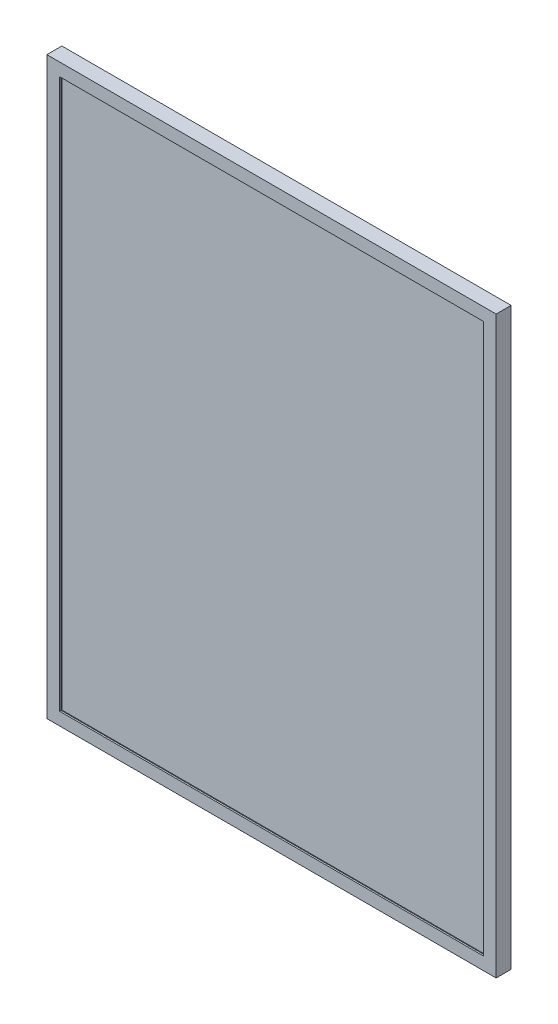
SolidWorks part; units mm, degrees
ref_plane "Front Plane" through (0, 0, 0) normal (0, 0, 1) x (1, 0, 0)
ref_plane "Top Plane" through (0, 0, 0) normal (0, 1, 0) x (1, 0, 0)
ref_plane "Right Plane" through (0, 0, 0) normal (1, 0, 0) x (0, 0, -1)
sketch "Sketch1" plane through (0, 0, 0) normal (0, 0, 1) x (1, 0, 0)
  line L1 (300, -384) -> (-300, -384)
  line L2 (300, -384) -> (300, 384)
  line L3 (300, 384) -> (-300, 384)
  line L4 (-300, -384) -> (-300, 384)
  line L5 (300, -384) -> (-300, 384) construction
  line L6 (300, 384) -> (-300, -384) construction
  point P0 (0, 0)
  dimension "D1" = 600
  dimension "D2" = 768
extrude "Boss-Extrude1" add sketch "Sketch1" along normal blind 20
shell "Shell1" thickness 2
sketch "Sketch2" plane through (0, 0, 20) normal (0, 0, 1) x (1, 0, 0)
  line L1 (-298, 382) -> (298, 382)
  line L2 (-298, 382) -> (-298, -382)
  line L3 (-298, -382) -> (298, -382)
  line L4 (298, 382) -> (298, -382)
  line L5 (-283, 367) -> (283, 367)
  line L6 (-283, 367) -> (-283, -367)
  line L7 (-283, -367) -> (283, -367)
  line L8 (283, 367) -> (283, -367)
  dimension "D1" = 15
  dimension "D2" = 15
  dimension "D3" = 15
  dimension "D4" = 15
extrude "Boss-Extrude2" add sketch "Sketch2" against normal blind 2
